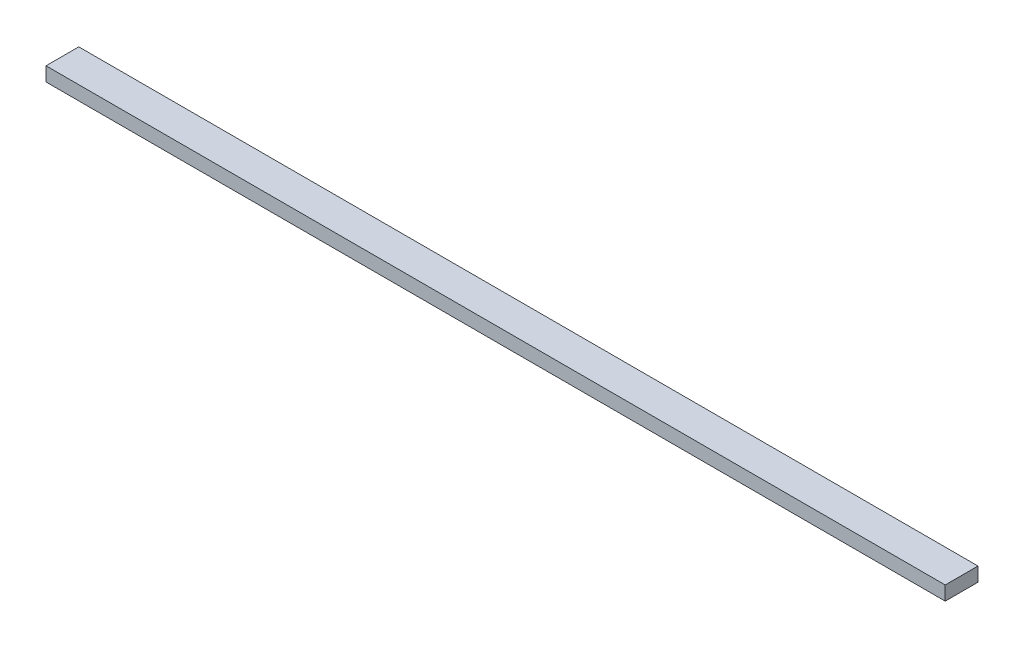
SolidWorks part; units mm, degrees
ref_plane "Front Plane" through (0, 0, 0) normal (0, 0, 1) x (1, 0, 0)
ref_plane "Top Plane" through (0, 0, 0) normal (0, 1, 0) x (1, 0, 0)
ref_plane "Right Plane" through (0, 0, 0) normal (1, 0, 0) x (0, 0, -1)
sketch "Sketch1" plane through (0, 0, 0) normal (0, 1, 0) x (1, 0, 0)
  line L1 (0, 0) -> (2438.4, 0)
  line L2 (0, 0) -> (0, -88.9)
  line L3 (0, -88.9) -> (2438.4, -88.9)
  line L4 (2438.4, 0) -> (2438.4, -88.9)
extrude "Boss-Extrude1" add sketch "Sketch1" along normal blind 38.1
sketch "Sketch2" plane through (0, 38.1, 0) normal (0, 1, 0) x (1, 0, 0)
  line L0 (0, -44.45) -> (812.8, -44.45) construction
  line L1 (0, 0) -> (0, -88.9) construction
  line L2 (812.8, -44.45) -> (1625.6, -44.45) construction
  line L3 (1625.6, -44.45) -> (2438.4, -44.45) construction
  line L4 (2438.4, -88.9) -> (2438.4, 0) construction
  line L5 (812.8, 0) -> (812.8, -88.9) construction
  line L6 (2438.4, 0) -> (0, 0) construction
  line L7 (0, -88.9) -> (2438.4, -88.9) construction
  line L8 (1625.6, 0) -> (1625.6, -88.9) construction
sketch "Sketch3" plane through (0, 0, 0) normal (0, -1, 0) x (1, 0, 0)
  line L0 (0, 44.45) -> (812.8, 44.45) construction
  line L1 (812.8, 44.45) -> (1625.6, 44.45) construction
  line L2 (1625.6, 44.45) -> (2438.4, 44.45) construction
  line L3 (812.8, 88.9) -> (812.8, 0) construction
  line L4 (1625.6, 88.9) -> (1625.6, 0) construction
